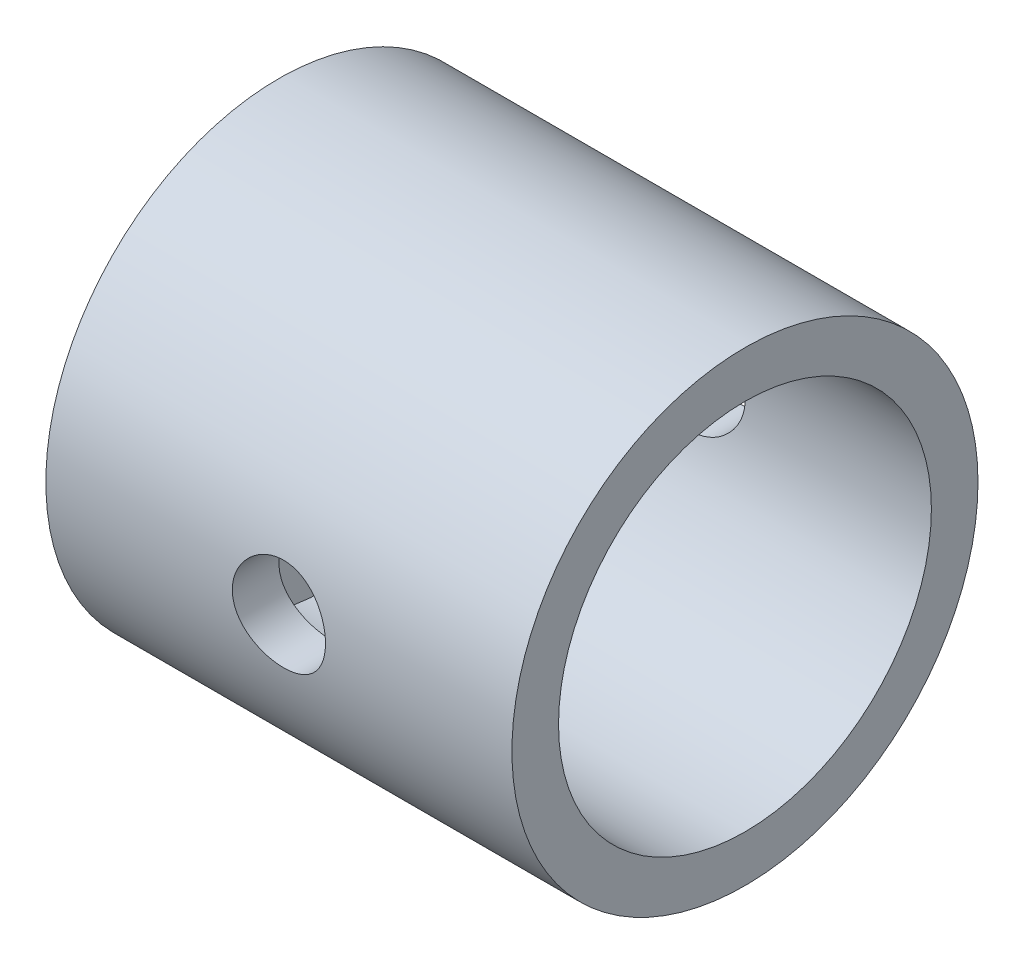
SolidWorks part; units mm, degrees
material "Plain Carbon Steel"
ref_plane "Front Plane" through (0, 0, 0) normal (0, 0, 1) x (1, 0, 0)
ref_plane "Top Plane" through (0, 0, 0) normal (0, 1, 0) x (1, 0, 0)
ref_plane "Right Plane" through (0, 0, 0) normal (1, 0, 0) x (0, 0, -1)
sketch "Sketch1" plane through (0, 0, 0) normal (1, 0, 0) x (0, 0, -1)
  circle A0 centre (0, 0) radius 37.5
  dimension "D1" = 75
extrude "Boss-Extrude1" add sketch "Sketch1" along normal blind 75
shell "Shell1" thickness 7.5
sketch "Sketch2" plane through (0, 0, 0) normal (0, 0, 1) x (1, 0, 0)
  line L0 (0, 0) -> (75, 0) construction
  line L1 (75, -37.5) -> (75, 37.5) construction
  circle A0 centre (37.5, 0) radius 7.5
  dimension "D1" = 15
extrude "Cut-Extrude1" cut sketch "Sketch2" against normal through all both and the other way through all
